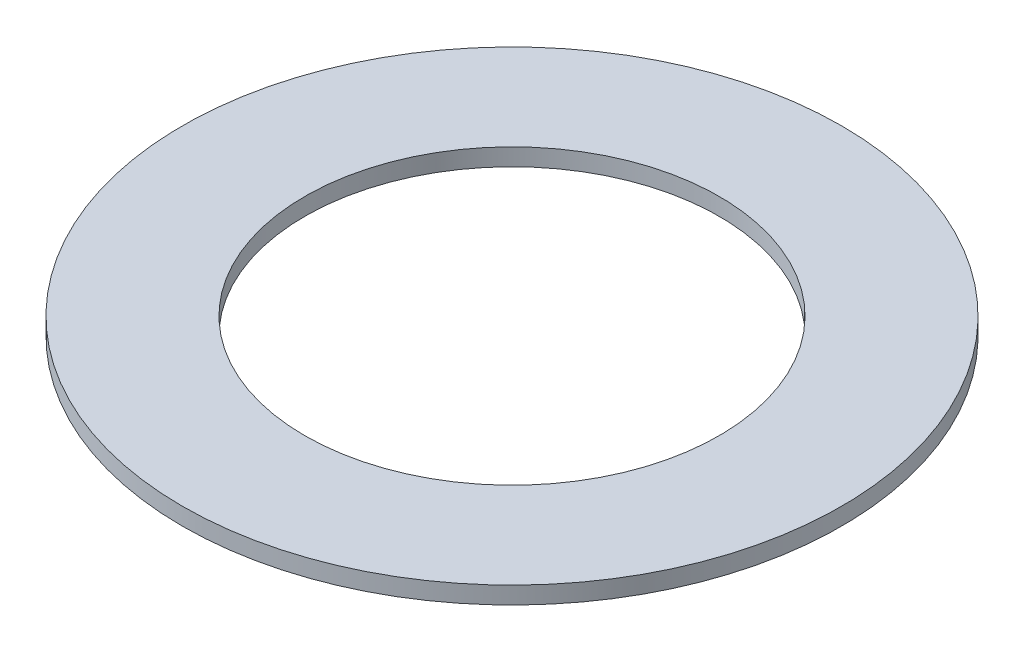
SolidWorks part; units mm, degrees
ref_plane "Face" through (0, 0, 0) normal (0, 0, 1) x (1, 0, 0)
ref_plane "Dessus" through (0, 0, 0) normal (0, 1, 0) x (1, 0, 0)
ref_plane "Droite" through (0, 0, 0) normal (1, 0, 0) x (0, 0, -1)
sketch "Esquisse1" plane through (0, 0, 0) normal (0, 1, 0) x (1, 0, 0)
  circle A0 centre (0, 0) radius 5.725
  circle A1 centre (0, 0) radius 3.6
  dimension "D1" = 11.45
  dimension "D2" = 7.2
extrude "Boss.-Extru.1" add sketch "Esquisse1" along normal blind 0.3
